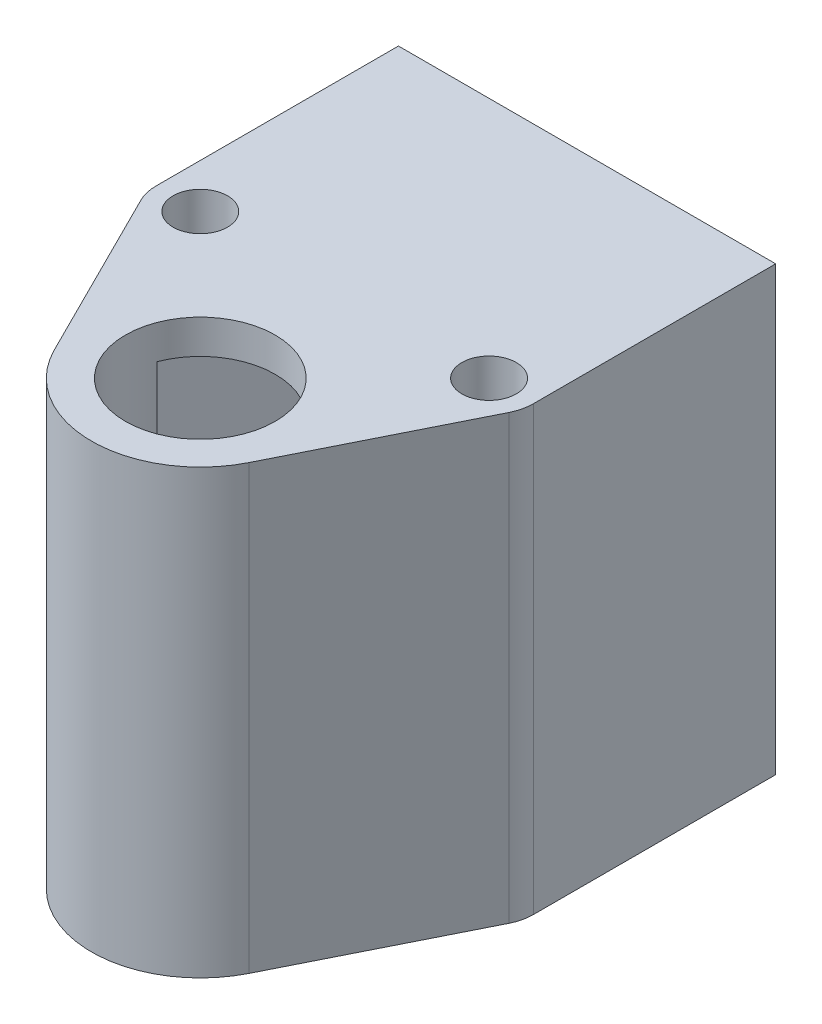
SolidWorks part; units mm, degrees
ref_plane "Front Plane" through (0, 0, 0) normal (0, 0, 1) x (1, 0, 0)
ref_plane "Top Plane" through (0, 0, 0) normal (0, 1, 0) x (1, 0, 0)
ref_plane "Right Plane" through (0, 0, 0) normal (1, 0, 0) x (0, 0, -1)
sketch "Sketch1" plane through (0, 0, 0) normal (0, 1, 0) x (1, 0, 0)
  line L0 (0, 50.9899) -> (0, -50.6959) construction
  line L1 (-34.8672, 34.8672) -> (0, 0) construction
  line L2 (-21.2132, 21.2132) -> (-14.9245, 21.2132) construction
  line L3 (14.3141, -7.1488) -> (27.0283, 18.309)
  line L4 (-10.2854, 3.9) -> (-22.7132, 50.2811)
  line L5 (-14.3141, -7.1488) -> (-27.0283, 18.309)
  line L6 (-27.7132, 56.8232) -> (-27.7132, 21.2132)
  line L7 (-22.7132, 50.2811) -> (-22.7132, 56.8232)
  line L8 (-27.7132, 56.8232) -> (-22.7132, 56.8232)
  line L9 (10.2854, 3.9) -> (22.7132, 50.2811)
  line L10 (21.2132, 21.2132) -> (14.9245, 21.2132) construction
  line L11 (27.7132, 56.8232) -> (22.7132, 56.8232)
  line L12 (22.7132, 50.2811) -> (22.7132, 56.8232)
  line L13 (27.7132, 56.8232) -> (27.7132, 21.2132)
  circle A1 centre (-21.2132, 21.2132) radius 4
  arc A9 (-27.7132, 21.2132) -> (-27.0283, 18.309) centre (-21.2132, 21.2132) ccw
  arc A11 (27.7132, 21.2132) -> (27.0283, 18.309) centre (21.2132, 21.2132) cw
  arc A12 (-10.2854, 3.9) -> (10.2854, 3.9) centre (0, 0) ccw
  arc A13 (-14.3141, -7.1488) -> (14.3141, -7.1488) centre (0, 0) ccw
  circle A14 centre (21.2132, 21.2132) radius 4
  point P18 (0, 0)
  dimension "D2" = 8
  dimension "D4" = 30
  dimension "D8" = 13
  dimension "D3" = 45
  dimension "D6" = 15
  dimension "D9" = 5
extrude "Boss-Extrude3" add sketch "Sketch1" along normal blind 55
sketch "Sketch4" plane through (0, 55, 0) normal (0, 1, 0) x (1, 0, 0)
  line L0 (-27.7132, 21.2132) -> (-27.7132, 56.8232)
  line L1 (-27.7132, 56.8232) -> (27.7132, 56.8232)
  line L2 (27.7132, 56.8232) -> (27.7132, 21.2132)
  line L3 (-14.3141, -7.1488) -> (-27.0283, 18.309)
  line L4 (-27.0283, 18.309) -> (-14.3141, -7.1488) construction
  line L5 (27.0283, 18.309) -> (14.3141, -7.1488)
  circle A0 centre (-21.2132, 21.2132) radius 4
  arc A1 (-27.7132, 21.2132) -> (-27.0283, 18.309) centre (-21.2132, 21.2132) ccw
  circle A2 centre (21.2132, 21.2132) radius 4
  arc A3 (27.0283, 18.309) -> (27.7132, 21.2132) centre (21.2132, 21.2132) ccw
  circle A4 centre (0, 0) radius 11
  arc A5 (-14.3141, -7.1488) -> (14.3141, -7.1488) centre (0, 0) ccw
extrude "Boss-Extrude4" add sketch "Sketch4" along normal blind 5 contours A3 L2 L1 L0 A1 L3 A5 L5
sketch "Sketch5" plane through (0, 0, 0) normal (0, -1, 0) x (1, 0, 0)
  line L0 (-27.0283, -18.309) -> (-14.3141, 7.1488)
  line L1 (14.3141, 7.1488) -> (27.0283, -18.309)
  line L2 (27.7132, -21.2132) -> (27.7132, -56.8232)
  line L3 (27.7132, -56.8232) -> (-27.7132, -56.8232)
  line L4 (-27.7132, -56.8232) -> (-27.7132, -21.2132)
  circle A0 centre (0, 0) radius 11
  arc A1 (14.3141, 7.1488) -> (-14.3141, 7.1488) centre (0, 0) ccw
  circle A2 centre (21.2132, -21.2132) radius 4
  arc A3 (27.7132, -21.2132) -> (27.0283, -18.309) centre (21.2132, -21.2132) ccw
  circle A4 centre (-21.2132, -21.2132) radius 4
  arc A5 (-27.0283, -18.309) -> (-27.7132, -21.2132) centre (-21.2132, -21.2132) ccw
extrude "Boss-Extrude5" add sketch "Sketch5" along normal blind 5 contours A5 L4 L3 L2 A3 L1 A1 L0
